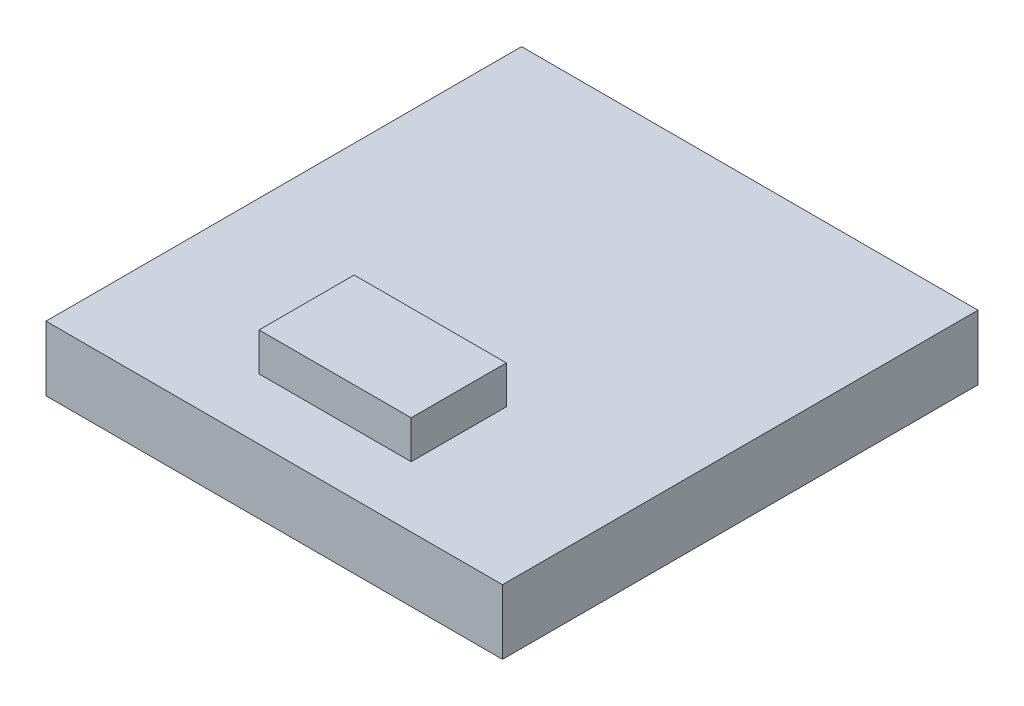
SolidWorks part; units mm, degrees
ref_plane "Front Plane" through (0, 0, 0) normal (0, 0, 1) x (1, 0, 0)
ref_plane "Top Plane" through (0, 0, 0) normal (0, 1, 0) x (1, 0, 0)
ref_plane "Right Plane" through (0, 0, 0) normal (1, 0, 0) x (0, 0, -1)
sketch "Sketch1" plane through (0, 0, 0) normal (0, 1, 0) x (1, 0, 0)
  line L1 (-3, 3.125) -> (3, 3.125)
  line L2 (-3, 3.125) -> (-3, -3.125)
  line L3 (-3, -3.125) -> (3, -3.125)
  line L4 (3, 3.125) -> (3, -3.125)
  point P4 (-3, 0)
  point P6 (0, 3.125)
  dimension "D1" = 0
  dimension "D2" = 0
  dimension "D3" = 6
  dimension "D4" = 6.25
extrude "Boss-Extrude1" add sketch "Sketch1" along normal blind 0.85
sketch "Sketch2" plane through (0, 0.85, 0) normal (0, 1, 0) x (1, 0, 0)
  line L0 (-3, -3.125) -> (3, -3.125) construction
  line L1 (-1, -2.325) -> (1, -2.325)
  line L2 (-1, -2.325) -> (-1, -1.075)
  line L3 (-1, -1.075) -> (1, -1.075)
  line L4 (1, -2.325) -> (1, -1.075)
  point P4 (0, -1.075)
  dimension "D1" = 0
  dimension "D2" = 2
  dimension "D3" = 1.25
  dimension "D4" = 0.8
extrude "Boss-Extrude2" add sketch "Sketch2" along normal blind 0.5
